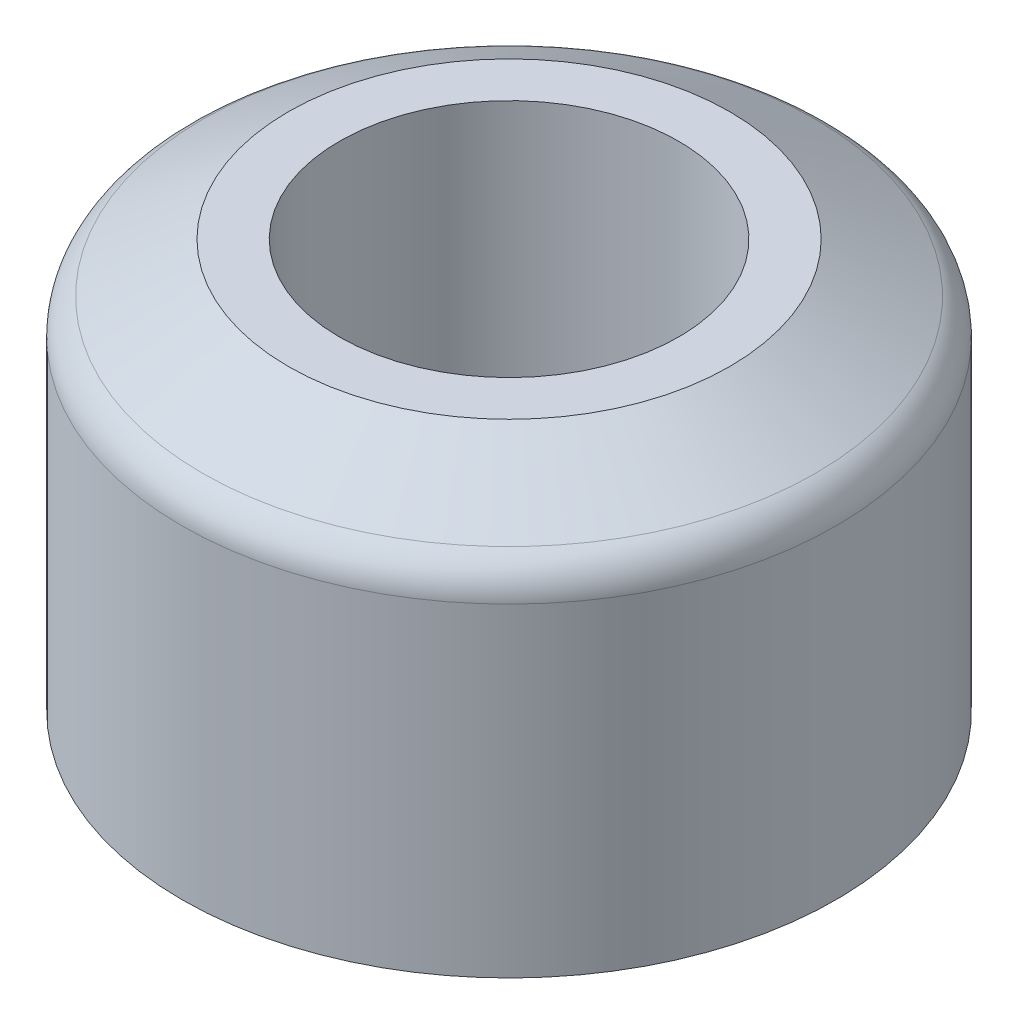
SolidWorks part; units mm, degrees
ref_plane "Front Plane" through (0, 0, 0) normal (0, 0, 1) x (1, 0, 0)
ref_plane "Top Plane" through (0, 0, 0) normal (0, 1, 0) x (1, 0, 0)
ref_plane "Right Plane" through (0, 0, 0) normal (1, 0, 0) x (0, 0, -1)
sketch "Sketch1" plane through (0, 0, 0) normal (0, 1, 0) x (1, 0, 0)
  circle A0 centre (0, 0) radius 4.15
  circle A1 centre (0, 0) radius 8
  dimension "D1" = 8.3
  dimension "D2" = 16
extrude "Boss-Extrude1" add sketch "Sketch1" along normal blind 10
chamfer "Chamfer1" distance 2.6 angle 30 1 edges at (0, 10, 8)
fillet "Fillet1" radius 1 1 edges at (0, 8.4989, 8)
